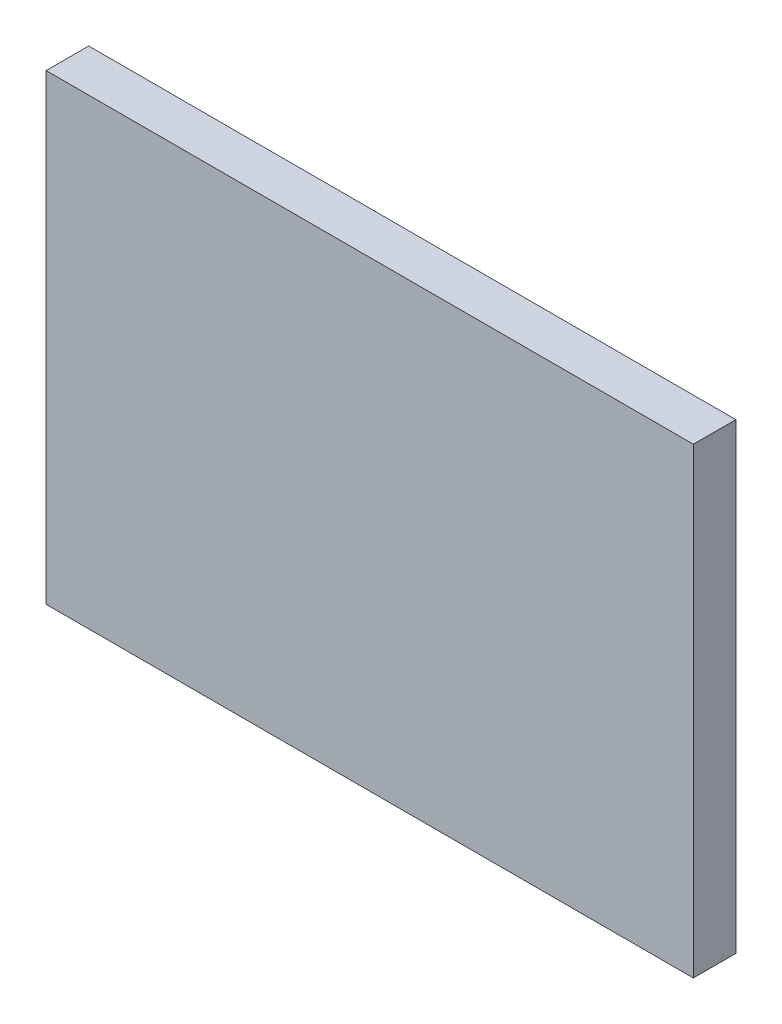
SolidWorks part; units mm, degrees
ref_plane "前视基准面" through (0, 0, 0) normal (0, 0, 1) x (1, 0, 0)
ref_plane "上视基准面" through (0, 0, 0) normal (0, 1, 0) x (1, 0, 0)
ref_plane "右视基准面" through (0, 0, 0) normal (1, 0, 0) x (0, 0, -1)
sketch "草图1" plane through (0, 0, 0) normal (0, 0, 1) x (1, 0, 0)
  line L0 (91.115, 49.0632) -> (126.115, 49.0632)
  line L1 (91.115, 74.0632) -> (126.115, 74.0632)
  line L2 (91.115, 74.0632) -> (91.115, 49.0632)
  line L3 (126.115, 74.0632) -> (126.115, 49.0632)
  dimension "D1" = 35
  dimension "D2" = 25
extrude "凸台-拉伸1" add sketch "草图1" along normal blind 2.3
